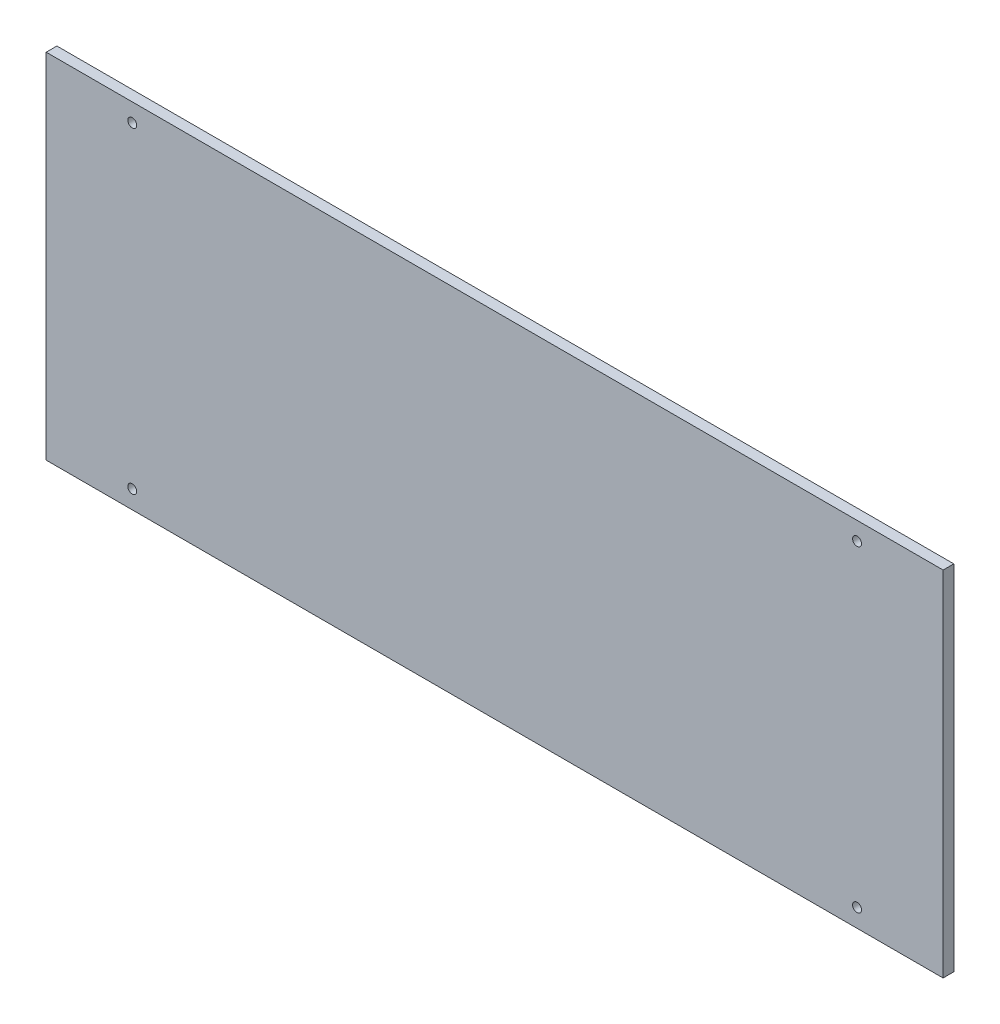
SolidWorks part; units mm, degrees
material "Acrylic (Medium-high impact)"
ref_plane "Front Plane" through (0, 0, 0) normal (0, 0, 1) x (1, 0, 0)
ref_plane "Top Plane" through (0, 0, 0) normal (0, 1, 0) x (1, 0, 0)
ref_plane "Right Plane" through (0, 0, 0) normal (1, 0, 0) x (0, 0, -1)
sketch "Sketch1" plane through (0, 0, 0) normal (0, 0, 1) x (1, 0, 0)
  line L1 (125.73, 49.53) -> (-125.73, 49.53)
  line L2 (125.73, 49.53) -> (125.73, -49.53)
  line L3 (125.73, -49.53) -> (-125.73, -49.53)
  line L4 (-125.73, 49.53) -> (-125.73, -49.53)
  line L5 (125.73, 49.53) -> (-125.73, -49.53) construction
  line L6 (125.73, -49.53) -> (-125.73, 49.53) construction
  line L7 (101.6, -44.45) -> (-101.6, -44.45) construction
  line L8 (101.6, -44.45) -> (101.6, 44.45) construction
  line L9 (101.6, 44.45) -> (-101.6, 44.45) construction
  line L10 (-101.6, -44.45) -> (-101.6, 44.45) construction
  line L11 (101.6, -44.45) -> (-101.6, 44.45) construction
  line L12 (101.6, 44.45) -> (-101.6, -44.45) construction
  circle A0 centre (-101.6, 44.45) radius 1.25
  circle A1 centre (101.6, 44.45) radius 1.25
  circle A2 centre (101.6, -44.45) radius 1.25
  circle A3 centre (-101.6, -44.45) radius 1.25
  point P0 (0, 0)
  point P5 (0, 0)
  dimension "D5" = 2.5
  dimension "D1" = 99.06
  dimension "D2" = 251.46
  dimension "D3" = 203.2
  dimension "D4" = 88.9
extrude "Boss-Extrude1" add sketch "Sketch1" along normal blind 3
